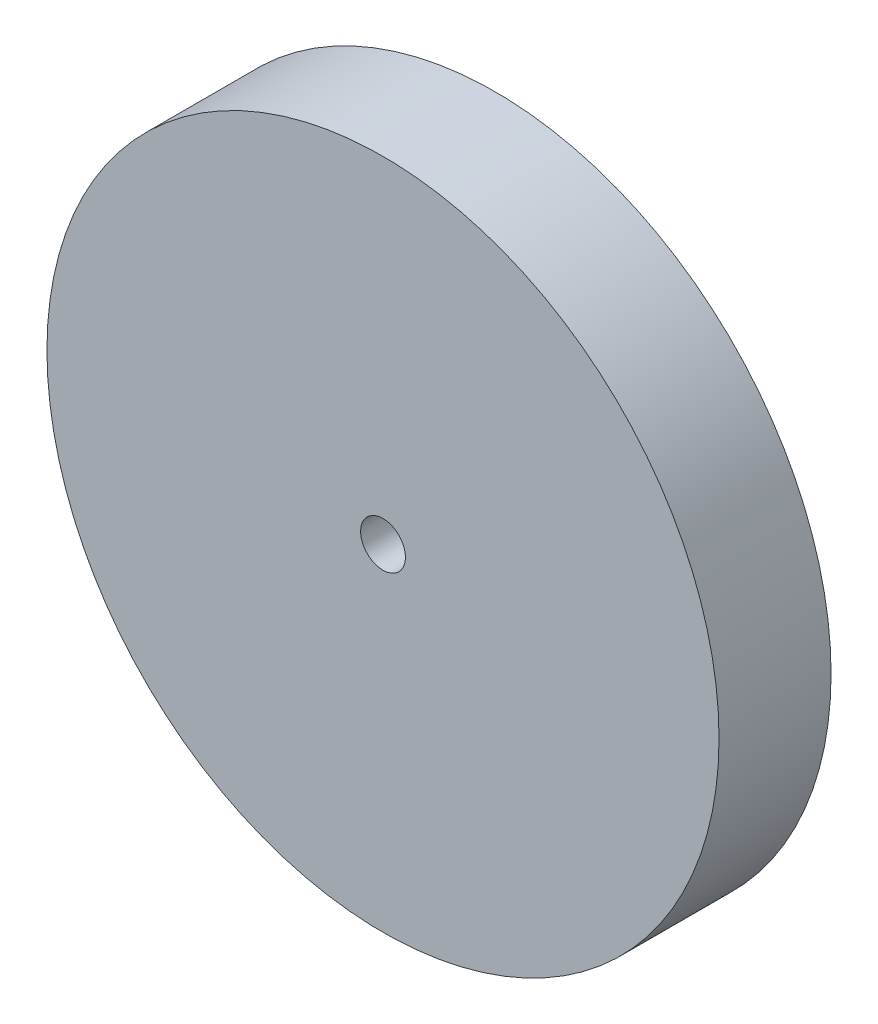
SolidWorks part; units mm, degrees
ref_plane "Ön Düzlem" through (0, 0, 0) normal (0, 0, 1) x (1, 0, 0)
ref_plane "Üst Düzlem" through (0, 0, 0) normal (0, 1, 0) x (1, 0, 0)
ref_plane "Sağ Düzlem" through (0, 0, 0) normal (1, 0, 0) x (0, 0, -1)
sketch "Çizim1" plane through (0, 0, 0) normal (0, 0, 1) x (1, 0, 0)
  circle A0 centre (0, 0) radius 60
  circle A1 centre (0, 0) radius 4
  dimension "D1" = 120
  dimension "D2" = 8
extrude "Yükseklik-Ekstrüzyon1" add sketch "Çizim1" along normal blind 20
